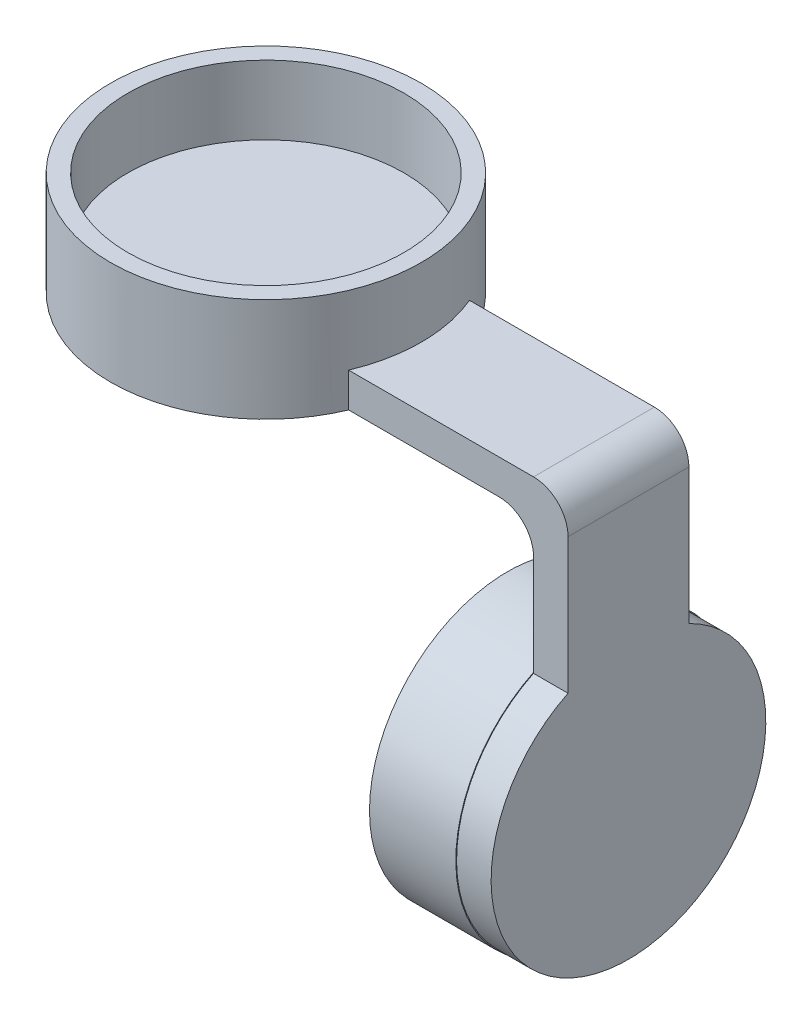
SolidWorks part; units mm, degrees
ref_plane "Front Plane" through (0, 0, 0) normal (0, 0, 1) x (1, 0, 0)
ref_plane "Top Plane" through (0, 0, 0) normal (0, 1, 0) x (1, 0, 0)
ref_plane "Right Plane" through (0, 0, 0) normal (1, 0, 0) x (0, 0, -1)
sketch "Sketch1" plane through (0, 0, 0) normal (1, 0, 0) x (0, 0, -1)
  circle A0 centre (0, 0) radius 14
  circle A1 centre (0, 0) radius 16
extrude "Boss-Extrude1" add sketch "Sketch1" against normal blind 10
sketch "Sketch2" plane through (0, 0, 0) normal (1, 0, 0) x (0, 0, -1)
  line L0 (-7, 14.2889) -> (-7, 20)
  line L3 (-7, 20) -> (7, 20)
  line L7 (7, 14.2889) -> (7, 20)
  arc A0 (-7, 14.2889) -> (7, 14.2889) centre (0, 0) ccw
  dimension "D2" = 7
  dimension "D1" = 20
  dimension "D3" = 7
extrude "Boss-Extrude2" add sketch "Sketch2" along normal blind 4
sketch "Sketch3" plane through (0, 0, -7) normal (0, 0, -1) x (-1, 0, 0)
  line L0 (0, 20) -> (-4, 20)
  line L1 (-4, 20) -> (-4, 30)
  line L5 (4, 30) -> (38, 30)
  line L6 (0, 34) -> (38, 34)
  line L7 (38, 34) -> (38, 30)
  line L8 (0, 26) -> (0, 20)
  arc A0 (0, 26) -> (4, 30) centre (4, 26) cw
  arc A1 (-4, 30) -> (0, 34) centre (0, 30) cw
  dimension "D1" = 4
  dimension "D2" = 4
  dimension "D3" = 42
  dimension "D4" = 10
extrude "Boss-Extrude3" add sketch "Sketch3" against normal blind 14
sketch "Sketch4" plane through (0, 34, 0) normal (0, 1, 0) x (1, 0, 0)
  line L0 (-38, -7) -> (-38, 7) construction
  circle A0 centre (-38, 0) radius 18
extrude "Boss-Extrude4" add sketch "Sketch4" against normal blind 4
sketch "Sketch5" plane through (0, 34, 0) normal (0, 1, 0) x (1, 0, 0)
  circle A0 centre (-38, 0) radius 18
  circle A1 centre (-38, 0) radius 16
extrude "Boss-Extrude5" add sketch "Sketch5" along normal blind 8
